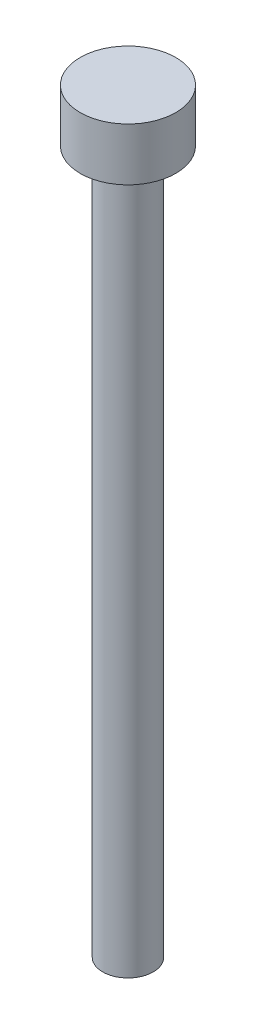
SolidWorks part; units mm, degrees
ref_plane "Front Plane" through (0, 0, 0) normal (0, 0, 1) x (1, 0, 0)
ref_plane "Top Plane" through (0, 0, 0) normal (0, 1, 0) x (1, 0, 0)
ref_plane "Right Plane" through (0, 0, 0) normal (1, 0, 0) x (0, 0, -1)
sketch "Sketch1" plane through (0, 0, 0) normal (0, 1, 0) x (1, 0, 0)
  circle A0 centre (0, 0) radius 2.72
  dimension "D1" = 5.44
extrude "Boss-Extrude1" add sketch "Sketch1" along normal blind 3
sketch "Sketch2" plane through (0, 0, 0) normal (0, -1, 0) x (1, 0, 0)
  circle A0 centre (0, 0) radius 1.44
  dimension "D1" = 2.88
extrude "Boss-Extrude2" add sketch "Sketch2" along normal blind 40
